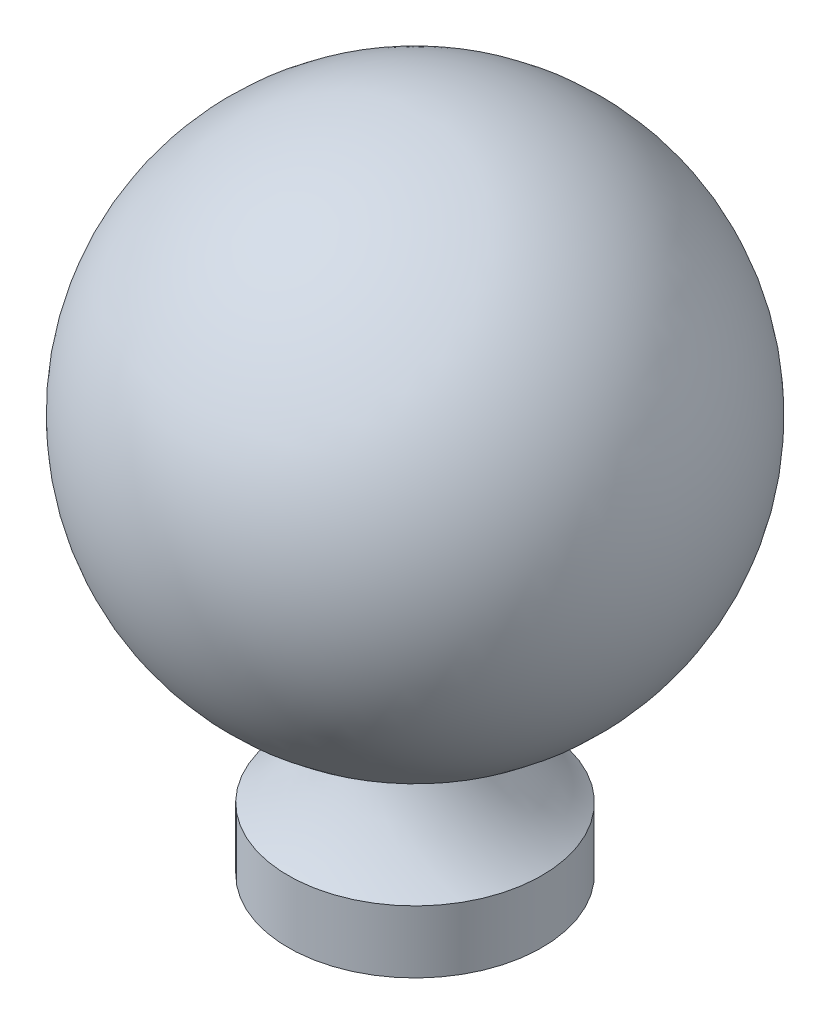
SolidWorks part; units mm, degrees
ref_plane "Front Plane" through (0, 0, 0) normal (0, 0, 1) x (1, 0, 0)
ref_plane "Top Plane" through (0, 0, 0) normal (0, 1, 0) x (1, 0, 0)
ref_plane "Right Plane" through (0, 0, 0) normal (1, 0, 0) x (0, 0, -1)
sketch "Sketch1" plane through (0, 0, 0) normal (0, 0, 1) x (1, 0, 0)
  line L0 (0, 0) -> (0, 49.8818) construction
  line L1 (0, 0) -> (2.795, 0)
  line L2 (2.795, 0) -> (2.795, 1.3751)
  line L3 (0, 14.52) -> (0, 0)
  arc A0 (1.5621, 3.2363) -> (0, 14.52) centre (0, 8.77) ccw
  arc A1 (2.795, 1.3751) -> (1.5283, 3.1724) centre (5.1349, 4.3693) cw
  arc A2 (1.5621, 3.2363) -> (1.5283, 3.1724) centre (1.5757, 3.1881) ccw
  dimension "D1" = 8.77
  dimension "D3" = 11.5
  dimension "D4" = 3.8
  dimension "D5" = 0.05
  dimension "D2" = 5.59
revolve "Revolve1" add sketch "Sketch1" angle 360 about L0
